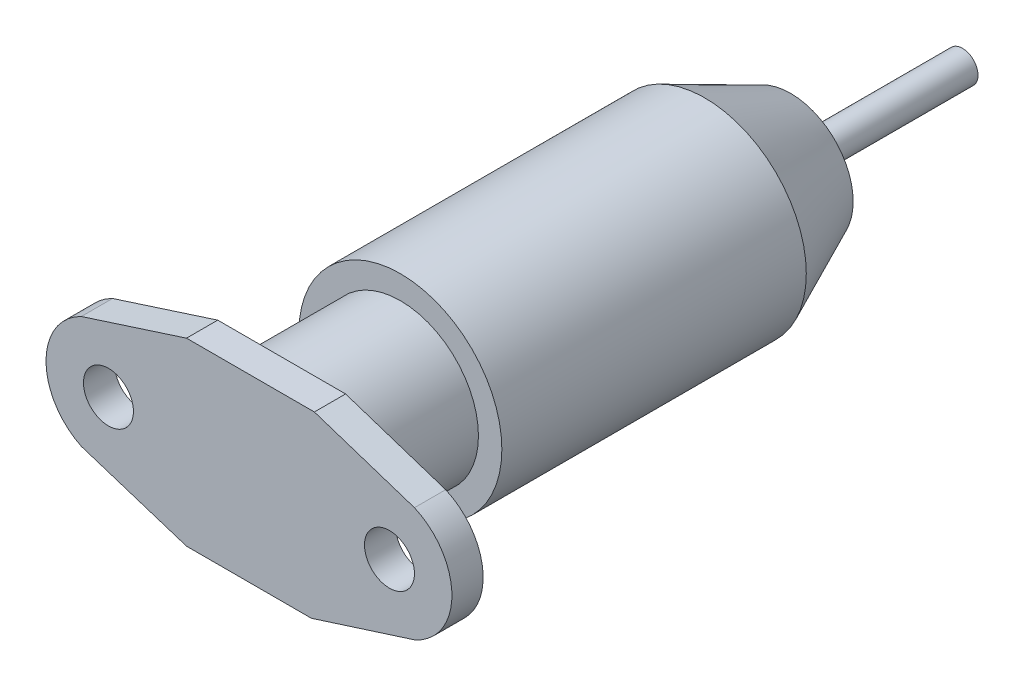
SolidWorks part; units mm, degrees
ref_plane "前视基准面" through (0, 0, 0) normal (0, 0, 1) x (1, 0, 0)
ref_plane "上视基准面" through (0, 0, 0) normal (0, 1, 0) x (1, 0, 0)
ref_plane "右视基准面" through (0, 0, 0) normal (1, 0, 0) x (0, 0, -1)
sketch "草图1" plane through (0, 0, 0) normal (0, 0, 1) x (1, 0, 0)
  line L1 (-7.2569, 5.3046) -> (0.9332, 5.3046)
  line L3 (-7.2569, -6.2354) -> (0.7431, -6.2354)
  line L10 (-7.2569, 5.3046) -> (-13.994, 3.1377)
  line L11 (-7.2569, -6.2354) -> (-13.994, -4.0685)
  line L12 (0.7431, -6.2354) -> (7.3444, -4.1309)
  line L13 (0.9332, 5.3046) -> (7.3444, 3.2001)
  circle A0 centre (-12.2569, -0.4654) radius 1.6
  circle A1 centre (5.7431, -0.4654) radius 1.6
  arc A2 (7.3444, 3.2001) -> (7.3444, -4.1309) centre (5.7431, -0.4654) cw
  arc A3 (-13.2953, 3.3974) -> (-13.4257, -4.2909) centre (-12.2569, -0.4654) ccw
  point P31 (0, 0)
  point P32 (7.3622, 3.2001)
  dimension "D5" = 3.2
  dimension "D6" = 3.2
  dimension "D9" = 4
  dimension "D10" = 4
extrude "凸台-拉伸1" add sketch "草图1" along normal blind 2 contours L10 A3 L11 L3 L12 A2 L13 L1 A0 A1
sketch "草图2" plane through (0, 0, 0) normal (0, 0, -1) x (-1, 0, 0)
  circle A0 centre (3.2569, -0.4654) radius 5
  dimension "D1" = 10
extrude "凸台-拉伸2" add sketch "草图2" along normal blind 7.7
sketch "草图3" plane through (0, 0, -7.7) normal (0, 0, -1) x (-1, 0, 0)
  line L0 (8.2569, -0.4654) -> (-1.7431, -0.4654)
  circle A0 centre (3.2569, -0.4654) radius 5 construction
  circle A1 centre (3.2569, -0.4654) radius 6.5
  circle M1 centre (3.2569, -0.4654) radius 5
  dimension "D1" = 13
extrude "凸台-拉伸3" add sketch "草图3" along normal blind 19.5 contours A1 M1 | L0 M1 | L0 M1
ref_plane "基准面4" through (0, 0, -27.2) normal (0, 0, -1) x (-1, 0, 0)
ref_plane "基准面6" through (0, 0, -32.7) normal (0, 0, -1) x (-1, 0, 0)
sketch "草图4" plane through (0, 0, -32.7) normal (0, 0, -1) x (-1, 0, 0)
  circle A0 centre (3.2569, -0.4654) radius 4
  dimension "D1" = 8
loft "放样1" add profiles "草图4" section "草图4" section face at (-9.7569, -0.4654, -27.2)
sketch "草图5" plane through (0, 0, -32.7) normal (0, 0, -1) x (-1, 0, 0)
  circle A0 centre (3.2569, -0.4654) radius 1
  dimension "D1" = 2
extrude "凸台-拉伸4" add sketch "草图5" along normal blind 11
